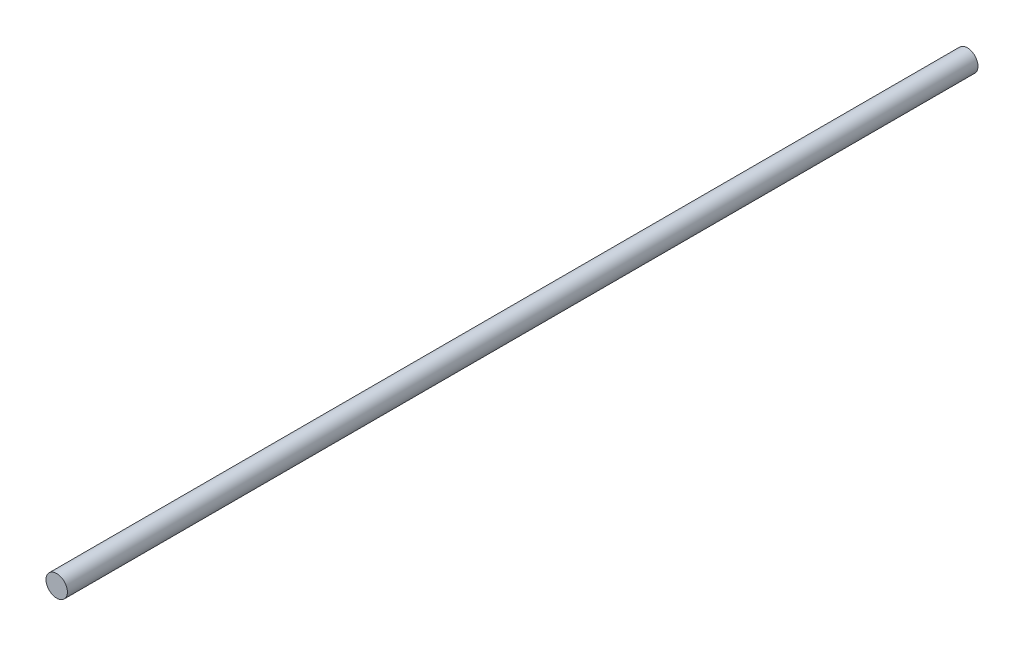
SolidWorks part; units mm, degrees
material "Oak"
ref_plane "Front Plane" through (0, 0, 0) normal (0, 0, 1) x (1, 0, 0)
ref_plane "Top Plane" through (0, 0, 0) normal (0, 1, 0) x (1, 0, 0)
ref_plane "Right Plane" through (0, 0, 0) normal (1, 0, 0) x (0, 0, -1)
sketch "Sketch2" plane through (0, 0, 0) normal (0, 0, 1) x (1, 0, 0)
  circle A0 centre (0, 0) radius 3.175
  dimension "D1" = 6.35
extrude "Boss-Extrude2" add sketch "Sketch2" along normal blind 270
